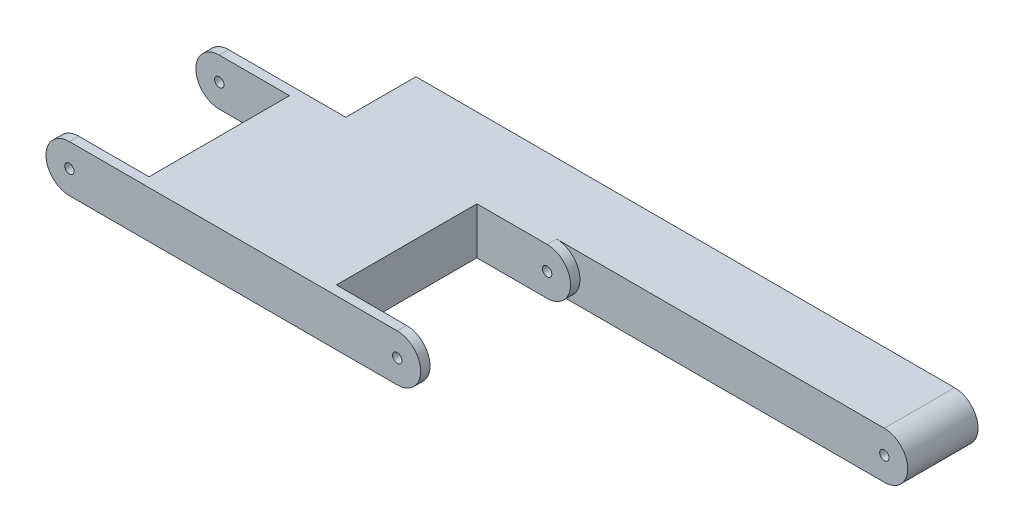
SolidWorks part; units mm, degrees
ref_plane "前基準面" through (0, 0, 0) normal (0, 0, 1) x (1, 0, 0)
ref_plane "上基準面" through (0, 0, 0) normal (0, 1, 0) x (1, 0, 0)
ref_plane "右基準面" through (0, 0, 0) normal (1, 0, 0) x (0, 0, -1)
sketch "草圖1" plane through (0, 0, 0) normal (0, 0, 1) x (1, 0, 0)
  line L0 (0, 47.1991) -> (0, -46.8309) construction
  line L1 (-71.1827, 0) -> (68.2665, 0) construction
  line L2 (-35, 0) -> (35, 0) construction
  line L3 (-35, 5) -> (35, 5)
  line L4 (-35, -5) -> (35, -5)
  arc A0 (-35, 5) -> (-35, -5) centre (-35, 0) ccw
  arc A1 (35, -5) -> (35, 5) centre (35, 0) ccw
  point P7 (0, 0)
  dimension "D2" = 5
  dimension "D1" = 70
extrude "填料-伸長1" add sketch "草圖1" along normal blind 34
sketch "草圖2" plane through (0, 0, 0) normal (0, 0, 1) x (1, 0, 0)
  line L0 (-45.1846, 0) -> (43.8227, 0) construction
  line L1 (0, 28.0802) -> (0, -27.5995) construction
  circle A0 centre (-35, 0) radius 1
  circle A1 centre (35, 0) radius 1
  dimension "D1" = 2
extrude "除料-伸長4" cut sketch "草圖2" against normal blind 30 and the other way through all
sketch "草圖3" plane through (0, 0, 0) normal (0, 1, 0) x (1, 0, 0)
  line L0 (35, 0) -> (-35, 0) construction
  line L1 (-40, -2) -> (-20, -2)
  line L2 (-40, -2) -> (-40, -32)
  line L3 (-40, -32) -> (-20, -32)
  line L4 (-20, -2) -> (-20, -32)
  line L5 (-35, -34) -> (-35, 0) construction
  line L6 (0, 16.8532) -> (0, -37.2241) construction
  line L7 (20, -2) -> (20, -32)
  line L8 (40, -32) -> (20, -32)
  line L9 (40, -2) -> (40, -32)
  line L10 (40, -2) -> (20, -2)
  dimension "D1" = 20
  dimension "D2" = 30
  dimension "D3" = 2
  dimension "D4" = 15
extrude "除料-伸長5" cut sketch "草圖3" against normal blind 30 and the other way blind 30
sketch "草圖4" plane through (0, 0, 0) normal (0, 0, 1) x (1, 0, 0)
  line L0 (0, 30.8378) -> (0, -29.7952) construction
  line L1 (-46.758, 0) -> (67.6106, 0) construction
  line L2 (35, 5) -> (-35, 5) construction
  line L3 (0, 5) -> (105, 5)
  line L4 (0, 5) -> (0, -5)
  line L5 (0, -5) -> (105, -5)
  line L6 (67.6106, 0) -> (119.1614, 0) construction
  arc A2 (105, -5) -> (105, 5) centre (105, 0) ccw
  dimension "D2" = 0
  dimension "D1" = 10
extrude "填料-伸長4" add sketch "草圖4" against normal blind 15
sketch "草圖5" plane through (0, 0, 0) normal (0, 0, 1) x (1, 0, 0)
  line L0 (132.2955, 0) -> (-55.3781, 0) construction
  line L1 (70, 38.422) -> (70, -46.2417)
  circle A0 centre (35, 0) radius 1
  circle A1 centre (105, 0) radius 1
  dimension "D2" = 2
  dimension "D1" = 35
extrude "除料-伸長7" cut sketch "草圖5" against normal through all contours A0 | A1
sketch "草圖6" plane through (0, 0, 0) normal (1, 0, 0) x (0, 0, -1)
  line L0 (23.7934, 0) -> (-11.2704, 0) construction
  line L1 (0, 16.6467) -> (0, -15.2206) construction
  line L3 (15, 5) -> (0, 5)
  line L4 (15, 5) -> (15, -5)
  line L5 (15, -5) -> (0, -5)
  line L6 (0, 5) -> (0, -5)
extrude "填料-伸長5" add sketch "草圖6" against normal blind 10
